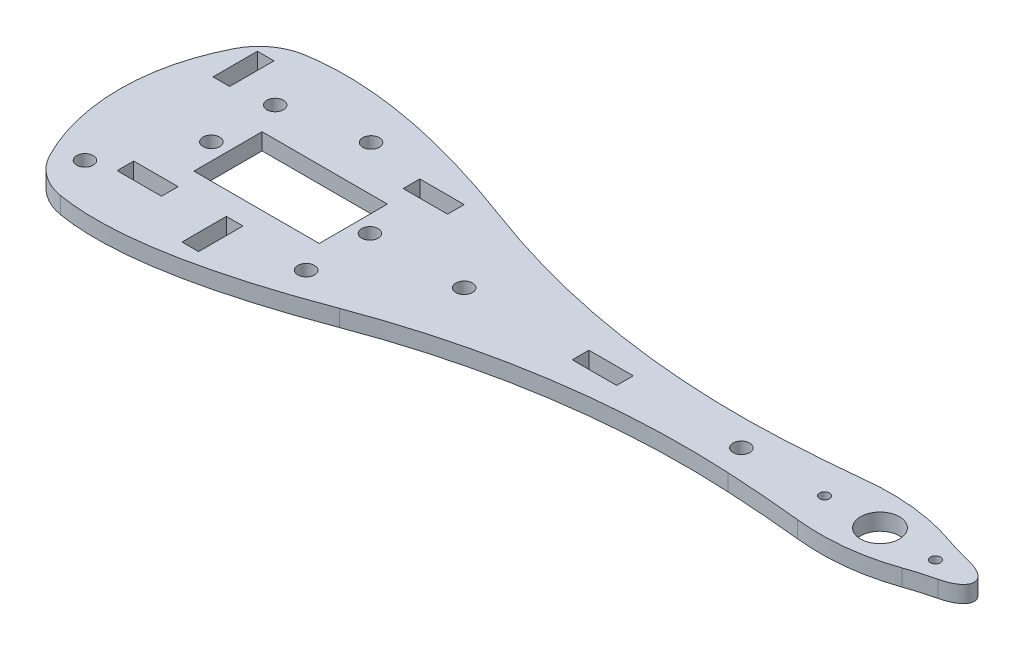
SolidWorks part; units mm, degrees
ref_plane "Plano frontal" through (0, 0, 0) normal (0, 0, 1) x (1, 0, 0)
ref_plane "Plano superior" through (0, 0, 0) normal (0, 1, 0) x (1, 0, 0)
ref_plane "Plano direito" through (0, 0, 0) normal (1, 0, 0) x (0, 0, -1)
sketch "Esboço1" plane through (0, 0, 0) normal (0, 1, 0) x (1, 0, 0)
  line L39 (-11.3, 6.15) -> (-11.3, -6.15)
  line L40 (-11.3, 6.15) -> (11.3, 6.15)
  line L41 (11.3, 6.15) -> (11.3, -6.15)
  line L42 (11.3, -6.15) -> (-11.3, -6.15)
  line L96 (-1.3, -10.3) -> (1.7, -10.3)
  line L97 (1.7, -10.3) -> (1.7, -18.3)
  line L98 (1.7, -18.3) -> (-1.3, -18.3)
  line L99 (-1.3, -18.3) -> (-1.3, -10.3)
  line L100 (-21.3, 10.3) -> (-24.3, 10.3)
  line L101 (-24.3, 10.3) -> (-24.3, 18.3)
  line L102 (-24.3, 18.3) -> (-21.3, 18.3)
  line L103 (-21.3, 18.3) -> (-21.3, 10.3)
  line L104 (10.3, 10) -> (10.3, 13)
  line L105 (10.3, 13) -> (18.3, 13)
  line L106 (18.3, 13) -> (18.3, 10)
  line L107 (18.3, 10) -> (10.3, 10)
  line L108 (-10.3, -10) -> (-10.3, -13)
  line L109 (-10.3, -13) -> (-18.3, -13)
  line L110 (-18.3, -13) -> (-18.3, -10)
  line L111 (-18.3, -10) -> (-10.3, -10)
  line L112 (11.3, 0) -> (6.3, 0)
  line L126 (56.3, -1.5) -> (60.3, -1.5)
  line L127 (60.3, -1.5) -> (60.3, 1.5)
  line L128 (60.3, 1.5) -> (52.3, 1.5)
  line L129 (52.3, 1.5) -> (52.3, -1.5)
  line L130 (52.3, -1.5) -> (56.3, -1.5)
  circle A2 centre (-14.3, 0) radius 1.5
  circle A3 centre (14.3, 0) radius 1.5
  circle A10 centre (0.2, 14.3) radius 1.5
  circle A11 centre (-22.8, -14.3) radius 1.5
  circle A12 centre (-14.3, 11.5) radius 1.5
  circle A13 centre (14.3, -11.5) radius 1.5
  circle A14 centre (106.3, 0) radius 3.5
  circle A17 centre (96.3, 0) radius 0.9
  circle A18 centre (116.3, 0) radius 0.9
  arc A24 (-26.7508, 16.7197) -> (-26.7508, -16.7197) centre (5.6027, 0) ccw
  arc A25 (-26.7508, 16.7197) -> (-19.544, 21.9871) centre (-17.8669, 12.1287) cw
  arc A26 (-26.7508, -16.7197) -> (-19.544, -21.9871) centre (-17.8669, -12.1287) ccw
  arc A27 (23.2473, 14.4669) -> (83.9533, 5.0794) centre (76.0379, 154.8705) ccw
  arc A28 (23.2473, -14.4669) -> (83.9533, -5.0794) centre (76.0379, -154.8705) cw
  arc A29 (119.5432, 2.8071) -> (114.5697, 4.2595) centre (131.0539, 51.464) cw
  arc A30 (114.5697, -4.2595) -> (119.5432, -2.8071) centre (131.0539, -51.464) cw
  circle A31 centre (31.3, 0) radius 1.5
  circle A33 centre (81.3, 0) radius 1.5
  ellipse E0 centre (116.3, 0) end of major axis (123.3, 0) minor radius 3.1675 (119.5432, -2.8071) -> (119.5432, 2.8071) ccw
  spline S0 degree 3 poles (114.5697, 4.2595) (109.1349, 6.1573) (103.4778, 6.7875) (97.5985, 6.15) knots 0.353889 0.353889 0.353889 0.353889 1 1 1 1
  spline S1 degree 3 poles (97.5985, 6.15) (93.039, 5.6761) (88.4906, 5.3192) (83.9533, 5.0794) knots 0 0 0 0 0.13796 0.13796 0.13796 0.13796
  spline S2 degree 3 poles (23.2473, 14.4669) (22.2154, 14.8549) (7.8436, 20.1288) (-8.0325, 23.9454) (-19.544, 21.9871) knots 0.189497 0.189497 0.189497 0.189497 0.21644 0.561127 0.561127 0.561127 0.561127
  spline S3 degree 3 poles (23.2473, -14.4669) (22.2154, -14.8549) (7.8436, -20.1288) (-8.0325, -23.9454) (-19.544, -21.9871) knots 0.189497 0.189497 0.189497 0.189497 0.21644 0.561127 0.561127 0.561127 0.561127
  spline S4 degree 3 poles (97.5985, -6.15) (93.039, -5.6761) (88.4906, -5.3192) (83.9533, -5.0794) knots 0 0 0 0 0.13796 0.13796 0.13796 0.13796
  spline S5 degree 3 poles (114.5697, -4.2595) (109.1349, -6.1573) (103.4778, -6.7875) (97.5985, -6.15) knots 0.353889 0.353889 0.353889 0.353889 1 1 1 1
  dimension "D1" = 10
  dimension "D2" = 10
  dimension "D3" = 150
  dimension "D4" = 150
  dimension "D5" = 50
  dimension "D6" = 50
extrude "Ressalto-extrusão1" add sketch "Esboço1" along normal blind 3 contours S5 A30 E0 A29 S0 S1 A27 S2 A25 A24 A26 S3 A28 S4 A18 A17 A14 A13 A12 A11 A10 A3 A2 L41 L42 L39 L40 L98 L99 L96 L97 L102 L103 L100 L101 L106 L107
